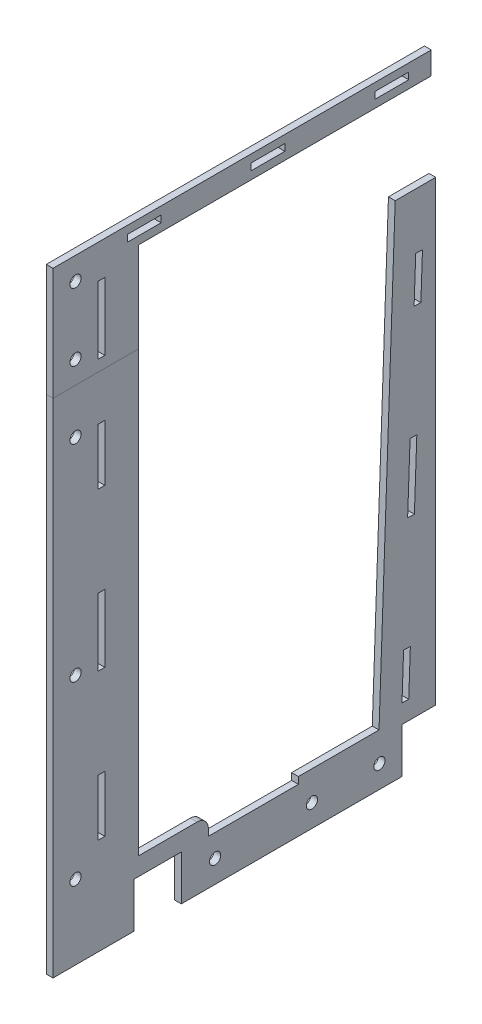
SolidWorks part; units mm, degrees
ref_plane "Front" through (0, 0, 0) normal (0, 0, 1) x (1, 0, 0)
ref_plane "Top" through (0, 0, 0) normal (0, 1, 0) x (1, 0, 0)
ref_plane "Right" through (0, 0, 0) normal (1, 0, 0) x (0, 0, -1)
sketch "Sketch1" plane through (0, 0, 0) normal (1, 0, 0) x (0, 0, -1)
  line L0 (66, 200) -> (66, 0) construction
  line L1 (0, 0) -> (132, 0)
  line L2 (0, 0) -> (0, 200)
  line L3 (0, 200) -> (132, 200)
  line L4 (132, 0) -> (132, 200)
  line L5 (0, 100) -> (132, 100) construction
  dimension "D1" = 200
  dimension "D2" = 132
extrude "Boss-Extrude1" add sketch "Sketch1" along normal blind 3
sketch "Sketch5" plane through (3, 0, 0) normal (1, 0, 0) x (0, 0, -1)
  line L0 (0, 200) -> (0, 0) construction
  line L1 (-23, 200) -> (147, 200)
  line L2 (-23, 200) -> (-23, -23)
  line L3 (-23, -23) -> (147, -23)
  line L4 (147, 200) -> (147, -23)
  line L6 (132, 0) -> (132, 200) construction
  line L7 (0, 0) -> (132, 0) construction
  line L8 (132, 200) -> (0, 200) construction
  dimension "D1" = 23
  dimension "D3" = 15
  dimension "D4" = 23
extrude "Boss-Extrude2" add sketch "Sketch5" against normal through all
sketch "Sketch2" plane through (3, 0, 0) normal (1, 0, 0) x (0, 0, -1)
  line L1 (135, 5.2) -> (132.0019, 5.3077)
  line L2 (135, 5.2) -> (135.7182, 25.1871)
  line L3 (135.7182, 25.1871) -> (132.7202, 25.2948)
  line L4 (132.0019, 5.3077) -> (132.7202, 25.2948)
  line L5 (138.1068, 175.1981) -> (141.1049, 175.0903)
  line L6 (142, 200) -> (135.7182, 25.1871) construction
  line L7 (138.1068, 175.1981) -> (137.3886, 155.211)
  line L8 (-23, -23) -> (147, -23) construction
  line L9 (147, -23) -> (147, 200) construction
  line L10 (135, -23) -> (135, 0.2) construction
  line L11 (135, 0.2) -> (135, 5.2) construction
  line L12 (147, 200) -> (-23, 200) construction
  line L13 (137.3886, 155.211) -> (140.3867, 155.1032)
  line L14 (141.1049, 175.0903) -> (140.3867, 155.1032)
  line L15 (135.593, 105.2432) -> (138.5911, 105.1355)
  line L16 (135.593, 105.2432) -> (134.5157, 75.2626)
  line L17 (134.5157, 75.2626) -> (137.5138, 75.1548)
  line L18 (138.5911, 105.1355) -> (137.5138, 75.1548)
  dimension "D2" = 5
  dimension "D3" = 20
  dimension "D4" = 3
  dimension "D1" = 12
  dimension "D5" = 23.2
  dimension "D6" = 5
  dimension "D7" = 30
  dimension "D8" = 20
  dimension "D9" = 50
  dimension "D10" = 50
extrude "Cut-Extrude1" cut sketch "Sketch2" against normal through all
sketch "Sketch3" plane through (3, 0, 0) normal (1, 0, 0) x (0, 0, -1)
  line L4 (-23, -23) -> (147, -23) construction
  line L5 (-23, 200) -> (-23, -23) construction
  line L6 (147, -23) -> (147, 200) construction
  circle A0 centre (122, -13) radius 2.5
  circle A1 centre (92, -13) radius 2.5
  circle A2 centre (-13, 10) radius 2.5
  circle A3 centre (49, -13) radius 2.5
  dimension "D1" = 5
  dimension "D2" = 5
  dimension "D3" = 5
  dimension "D8" = 5
  dimension "D4" = 33
  dimension "D7" = 10
  dimension "D5" = 25
  dimension "D6" = 30
  dimension "D9" = 72
  dimension "D10" = 10
extrude "Cut-Extrude2" cut sketch "Sketch3" against normal through all
sketch "Sketch6" plane through (3, 0, 0) normal (1, 0, 0) x (0, 0, -1)
  line L1 (13, -3) -> (34, -3)
  line L2 (13, -3) -> (13, -23)
  line L3 (13, -23) -> (34, -23)
  line L4 (34, -3) -> (34, -23)
  line L5 (-23, -23) -> (147, -23) construction
  circle A0 centre (122, -13) radius 2.5 construction
  dimension "D1" = 20
  dimension "D2" = 21
  dimension "D3" = 88
extrude "Cut-Extrude4" cut sketch "Sketch6" against normal through all
sketch "Sketch7" plane through (3, 0, 0) normal (1, 0, 0) x (0, 0, -1)
  line L1 (132, -3) -> (147, -3)
  line L2 (132, -3) -> (132, -23)
  line L3 (132, -23) -> (147, -23)
  line L4 (147, -3) -> (147, -23)
  circle A0 centre (122, -13) radius 2.5 construction
  dimension "D2" = 10
  dimension "D1" = 20
extrude "Cut-Extrude5" cut sketch "Sketch7" against normal through all
sketch "Sketch4" plane through (3, 0, 0) normal (1, 0, 0) x (0, 0, -1)
  line L0 (15, 200) -> (147, 200)
  line L1 (147, 200) -> (147, 30.2948)
  line L2 (132.7202, 25.2948) -> (132.0019, 5.3077) construction
  line L3 (128.9916, 200) -> (121.8048, 0)
  line L4 (15, 5) -> (41, 5)
  line L5 (15, 5) -> (15, 200)
  line L12 (147, 200) -> (-23, 200) construction
  line L13 (147, -3) -> (147, 200) construction
  line L15 (46, 0) -> (46, -3)
  line L16 (46, -3) -> (86, -3)
  line L17 (86, -3) -> (86, 0)
  line L18 (86, 0) -> (121.8048, 0)
  line L20 (147, -3) -> (147, 200) construction
  line L21 (34, -3) -> (13, -3) construction
  line L22 (0, 0) -> (0, 200) construction
  line L23 (66, 200) -> (66, 0) construction
  arc A0 (41, 5) -> (46, 0) centre (41, 0) cw
  point P19 (66, -3)
  dimension "D1" = 15
  dimension "D2" = 3
  dimension "D3" = 40
  dimension "D4" = 5
  dimension "D5" = 10
  dimension "D6" = 5
extrude "Cut-Extrude3" cut sketch "Sketch4" against normal through all contours L4 A0 L15 L16 L17 L18 L3 L0 L5
sketch "Sketch8" plane through (3, 0, 0) normal (1, 0, 0) x (0, 0, -1)
  line L0 (15, 200) -> (-23, 200) construction
  line L1 (-3, 180) -> (0, 180)
  line L2 (-3, 180) -> (-3, 155)
  line L3 (-3, 155) -> (0, 155)
  line L4 (0, 180) -> (0, 155)
  line L5 (-3, 115) -> (0, 115)
  line L6 (-3, 115) -> (-3, 85)
  line L7 (-3, 85) -> (0, 85)
  line L8 (0, 115) -> (0, 85)
  line L9 (-3, 45) -> (0, 45)
  line L10 (-3, 45) -> (-3, 20)
  line L11 (-3, 20) -> (0, 20)
  line L12 (0, 45) -> (0, 20)
  line L14 (-23, 200) -> (-23, -23) construction
  line L19 (0, 100) -> (132, 100) construction
  line L20 (0, 0) -> (132, 0) construction
  point P18 (-23, 88.5)
  point P19 (0, 100)
  dimension "D1" = 3
  dimension "D2" = 20
  dimension "D3" = 25
  dimension "D4" = 30
  dimension "D5" = 25
  dimension "D6" = 20
  dimension "D7" = 20
extrude "Cut-Extrude6" cut sketch "Sketch8" against normal through all
sketch "Sketch9" plane through (3, 0, 0) normal (1, 0, 0) x (0, 0, -1)
  line L0 (15, 200) -> (-23, 200) construction
  line L1 (-23, 200) -> (-23, -23) construction
  circle A0 centre (-13, 180) radius 2.5
  circle A1 centre (-13, 88.5) radius 2.5
  point P4 (-13, 10)
  point P10 (-23, 88.5)
  dimension "D1" = 5
  dimension "D2" = 5
  dimension "D3" = 20
extrude "Cut-Extrude7" cut sketch "Sketch9" against normal through all
sketch "Sketch10" plane through (3, 0, 0) normal (1, 0, 0) x (0, 0, -1)
  line L0 (-23, 200) -> (-23, 250)
  line L1 (-23, 250) -> (145, 250)
  line L2 (145, 250) -> (145, 240)
  line L3 (145, 240) -> (15, 240)
  line L4 (15, 240) -> (15, 200)
  line L5 (15, 5) -> (15, 200) construction
  line L6 (-23, 200) -> (15, 200)
  line L24 (15, 5) -> (15, 200)
  line L25 (15, 200) -> (-23, 200)
  line L26 (-23, 200) -> (-23, -23)
  line L27 (-23, -23) -> (13, -23)
  line L28 (13, -23) -> (13, -3)
  line L29 (13, -3) -> (34, -3)
  line L30 (34, -3) -> (34, -23)
  line L31 (34, -23) -> (132, -23)
  line L32 (132, -23) -> (132, -3)
  line L33 (132, -3) -> (147, -3)
  line L34 (147, -3) -> (147, 200)
  line L35 (147, 200) -> (128.9916, 200)
  line L36 (128.9916, 200) -> (121.8048, 0)
  line L37 (121.8048, 0) -> (86, 0)
  line L38 (86, 0) -> (86, -3)
  line L39 (86, -3) -> (46, -3)
  line L40 (46, -3) -> (46, 0)
  line L41 (41, 5) -> (15, 5)
  line L42 (15, 5) -> (15, 200)
  line L44 (-23, 200) -> (-23, -23)
  line L45 (-23, -23) -> (13, -23)
  line L46 (13, -23) -> (13, -3)
  line L47 (13, -3) -> (34, -3)
  line L48 (34, -3) -> (34, -23)
  line L49 (34, -23) -> (132, -23)
  line L50 (132, -23) -> (132, -3)
  line L51 (132, -3) -> (147, -3)
  line L52 (147, -3) -> (147, 200)
  line L53 (147, 200) -> (128.9916, 200)
  line L54 (128.9916, 200) -> (121.8048, 0)
  line L55 (121.8048, 0) -> (86, 0)
  line L56 (86, 0) -> (86, -3)
  line L57 (86, -3) -> (46, -3)
  line L58 (46, -3) -> (46, 0)
  line L59 (41, 5) -> (15, 5)
  arc A1 (46, 0) -> (41, 5) centre (41, 0) ccw
  arc A2 (46, 0) -> (41, 5) centre (41, 0) ccw
  line M20 (15, 200) -> (-23, 200)
  dimension "D1" = 10
  dimension "D2" = 40
  dimension "D3" = 130
  dimension "D4" = 0
extrude "Boss-Extrude3" add sketch "Sketch10" against normal blind 3 separate body contours L4 L3 L2 L1 L0 M20
sketch "Sketch11" plane through (3, 0, 0) normal (1, 0, 0) x (0, 0, -1)
  line L0 (145, 245) -> (0, 245) construction
  line L1 (135, 246.5) -> (120, 246.5)
  line L2 (135, 246.5) -> (135, 243.5)
  line L3 (135, 243.5) -> (120, 243.5)
  line L4 (120, 246.5) -> (120, 243.5)
  line L5 (80, 246.5) -> (65, 246.5)
  line L6 (80, 246.5) -> (80, 243.5)
  line L7 (80, 243.5) -> (65, 243.5)
  line L8 (65, 246.5) -> (65, 243.5)
  line L9 (25, 246.5) -> (10, 246.5)
  line L10 (25, 246.5) -> (25, 243.5)
  line L11 (25, 243.5) -> (10, 243.5)
  line L12 (10, 246.5) -> (10, 243.5)
  line L13 (145, 250) -> (145, 240) construction
  line L16 (0, 155) -> (0, 180) construction
  point P18 (10, 245)
  point P19 (72.5, 245)
  point P20 (72.5, 246.5)
  dimension "D1" = 3
  dimension "D2" = 15
  dimension "D3" = 15
  dimension "D4" = 15
  dimension "D5" = 10
  dimension "D6" = 10
extrude "Cut-Extrude8" cut sketch "Sketch11" against normal blind 3
sketch "Sketch12" plane through (3, 0, 0) normal (1, 0, 0) x (0, 0, -1)
  line L0 (-23, 250) -> (145, 250) construction
  line L1 (15, 200) -> (-23, 200) construction
  line L2 (-23, 200) -> (-23, 250) construction
  circle A0 centre (-13, 240) radius 2.5
  circle A1 centre (-13, 210) radius 2.5
  dimension "D1" = 5
  dimension "D2" = 5
  dimension "D5" = 10
  dimension "D3" = 10
  dimension "D4" = 10
extrude "Cut-Extrude9" cut sketch "Sketch12" against normal blind 10
sketch "Sketch13" plane through (3, 0, 0) normal (1, 0, 0) x (0, 0, -1)
  line L0 (15, 200) -> (-23, 200) construction
  line L1 (-3, 235) -> (0, 235)
  line L2 (-3, 235) -> (-3, 205)
  line L3 (-3, 205) -> (0, 205)
  line L4 (0, 235) -> (0, 205)
  line L5 (-3, 180) -> (-3, 155) construction
  dimension "D1" = 30
  dimension "D2" = 3
  dimension "D3" = 5
extrude "Cut-Extrude10" cut sketch "Sketch13" against normal blind 10
equation "\"D2@Sketch3\"=\"D1@Sketch3\""
equation "\"D3@Sketch3\"=\"D1@Sketch3\""
equation "\"D8@Sketch3\"=\"D1@Sketch3\""
equation "\"D2@Sketch9\"=\"D1@Sketch9\""
equation "\"D8@Sketch2\"=\"D3@Sketch2\""
equation "\"D3@Sketch11\"=\"D2@Sketch11\""
equation "\"D4@Sketch11\"=\"D2@Sketch11\""
equation "\"D2@Sketch12\"=\"D1@Sketch12\""
equation "\"D4@Sketch12\"=\"D3@Sketch12\""
